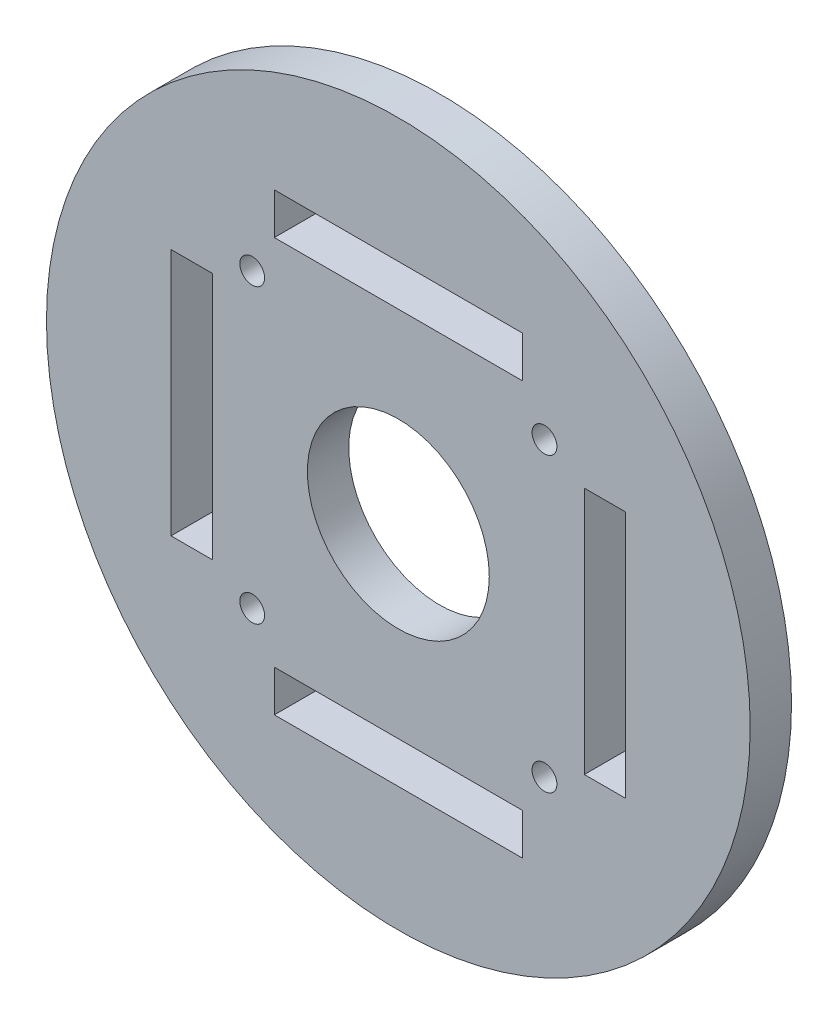
SolidWorks part; units mm, degrees
material "PMMA"
ref_plane "Front Plane" through (0, 0, 0) normal (0, 0, 1) x (1, 0, 0)
ref_plane "Top Plane" through (0, 0, 0) normal (0, 1, 0) x (1, 0, 0)
ref_plane "Right Plane" through (0, 0, 0) normal (1, 0, 0) x (0, 0, -1)
sketch "Schizzo1" plane through (0, 0, 0) normal (0, 0, 1) x (1, 0, 0)
  circle A1 centre (0, 0) radius 42.5627
  dimension "D2" = 85.1253
extrude "Estrusione-Estrusione1" add sketch "Schizzo1" along normal blind 5
sketch "Schizzo3" plane through (0, 0, 0) normal (0, 0, 1) x (1, 0, 0)
  circle A0 centre (0, 0) radius 11
  dimension "D1" = 22
extrude "Taglio-Estrusione2" cut sketch "Schizzo3" along direction (0, 0, 1) on the side of the normal through all
sketch "Schizzo4" plane through (0, 0, 0) normal (0, 0, 1) x (1, 0, 0)
  line L0 (-22.5, 15) -> (-22.5, -15)
  line L2 (0, 42.5627) -> (0, -42.5627) construction
  line L3 (42.5627, 0) -> (-42.5627, 0) construction
  line L4 (-27.5, 15) -> (-22.5, 15)
  line L5 (-15, 27.5) -> (-15, 22.5)
  line L6 (-27.5, 15) -> (-27.5, -15)
  line L7 (15, 27.5) -> (-15, 27.5)
  line L8 (15, 27.5) -> (15, 22.5)
  line L9 (15, 22.5) -> (-15, 22.5)
  line L10 (27.5, 15) -> (22.5, 15)
  line L11 (-27.5, -15) -> (-22.5, -15)
  line L12 (27.5, -15) -> (27.5, 15)
  line L13 (27.5, -15) -> (22.5, -15)
  line L14 (22.5, -15) -> (22.5, 15)
  line L15 (15, -27.5) -> (15, -22.5)
  line L16 (-15, -27.5) -> (15, -27.5)
  line L17 (-15, -27.5) -> (-15, -22.5)
  line L18 (-15, -22.5) -> (15, -22.5)
  line L19 (-17.6777, 17.6777) -> (17.6777, 17.6777) construction
  line L20 (17.6777, 17.6777) -> (17.6777, -17.6777) construction
  line L21 (17.6777, -17.6777) -> (-17.6777, -17.6777) construction
  circle A0 centre (0, 0) radius 42.5627 construction
  circle A9 centre (17.6777, 17.6777) radius 1.5
  circle A11 centre (17.6777, -17.6777) radius 1.5
  circle A13 centre (-17.6777, -17.6777) radius 1.5
  circle A15 centre (-17.6777, 17.6777) radius 1.5
  point P0 (0, 0)
  point P15 (0, 0)
  point P16 (0, 0)
  point P37 (0, 0)
  point P38 (0, 0)
  point P39 (0, 0)
  point P54 (0, 0)
  dimension "D1" = 5
  dimension "D8" = 3
  dimension "D2" = 30
  dimension "D3" = 22.5
  dimension "D4" = 15
  dimension "D6" = 17.6777
  dimension "D7" = 17.6777
  dimension "D9" = 35.3553
  dimension "D10" = 35.3553
  dimension "D11" = 35.3553
  dimension "D12" = 35.3553
  dimension "D5" = 4
extrude "Taglio-Estrusione3" cut sketch "Schizzo4" along direction (0, 0, 1) on the side of the normal through all
equation "\"PD\"= ( \"Pitch\" * \"N\" ) / 3.141593'Pitch Diameter"
equation "\"Pitch\"= 8"
equation "\"N\"= 32'Number of Teeth"
equation "\"OD\"= \"PD\" - 2 * \"U\"'Outer Diameter"
equation "\"h_t\"= 3.451mm'Height of the tooth"
equation "\"D2@Schizzo1\"=\"OD\"+5mm"
equation "\"U\"= 0.681'distance between the tensile cord and the bottom of the belt tooth"
equation "\"Thickness5\"=5"
equation "\"D1@Estrusione-Estrusione1\"=\"Thickness5\""
equation "\"D_t\"=5.14"
equation "\"R\"=0.15"
equation "\"R_t\"=0.8"
equation "\"ID\"= \"OD\" - 2 * \"h_t\""
equation "\"D1@Schizzo4\"=\"Thickness5\""
